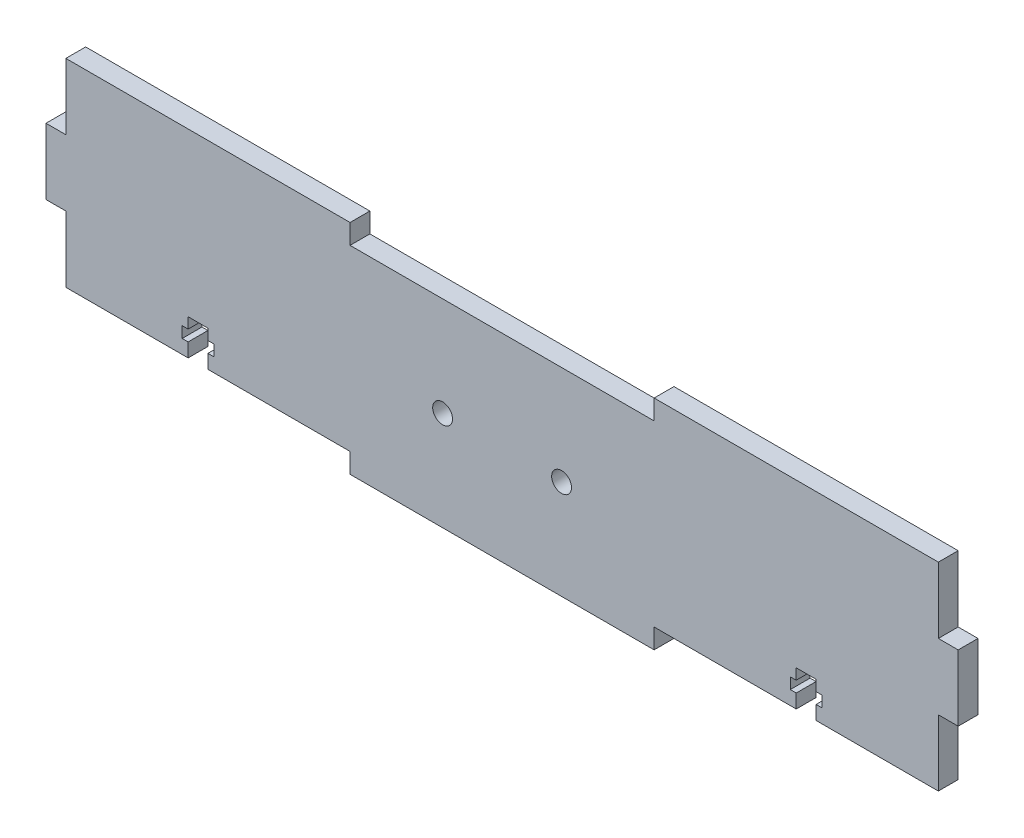
SolidWorks part; units mm, degrees
ref_plane "Alzado" through (0, 0, 0) normal (0, 0, 1) x (1, 0, 0)
ref_plane "Planta" through (0, 0, 0) normal (0, 1, 0) x (1, 0, 0)
ref_plane "Vista lateral" through (0, 0, 0) normal (1, 0, 0) x (0, 0, -1)
sketch "Croquis1" plane through (0, 0, 0) normal (0, 0, 1) x (1, 0, 0)
  line L0 (115, 0) -> (115, 23.3303) construction
  line L1 (0, 0) -> (230, 0)
  line L2 (0, 0) -> (0, 55)
  line L3 (0, 55) -> (230, 55)
  line L4 (230, 0) -> (230, 55)
  line L5 (0, 55) -> (5, 55)
  line L6 (0, 55) -> (0, 0)
  line L7 (0, 0) -> (5, 0)
  line L8 (5, 55) -> (5, 0)
  line L9 (225, 55) -> (225, 0)
  line L10 (76.6667, 5) -> (76.6667, 0)
  line L11 (0, 0) -> (230, 0)
  line L12 (0, 0) -> (0, 5)
  line L13 (0, 5) -> (230, 5)
  line L14 (230, 0) -> (230, 5)
  line L15 (153.3333, 0) -> (153.3333, 5)
  line L16 (0, 38.3333) -> (5, 38.3333)
  line L17 (5, 21.6667) -> (0, 21.6667)
  line L18 (225, 21.6667) -> (230, 21.6667)
  line L19 (230, 38.3333) -> (225, 38.3333)
  point P21 (2.5, 38.3333)
  dimension "D1" = 230
  dimension "D2" = 55
  dimension "D3" = 5
  dimension "D4" = 5
  dimension "D5" = 76.6667
  dimension "D6" = 76.6667
  dimension "D7" = 16.6667
  dimension "D8" = 16.6667
extrude "Saliente-Extruir1" add sketch "Croquis1" along normal blind 5
sketch "Croquis2" plane through (0, 0, 5) normal (0, 0, 1) x (1, 0, 0)
  line L0 (38.3333, 5) -> (38.3333, 14) construction
  line L1 (5, 5) -> (76.6667, 5) construction
  line L2 (115, 0) -> (115, 11.3726) construction
  line L3 (76.6667, 0) -> (153.3333, 0) construction
  line L4 (35.8333, 5) -> (35.8333, 8.5)
  line L5 (35.8333, 8.5) -> (34.3333, 8.5)
  line L6 (34.3333, 8.5) -> (34.3333, 11.3)
  line L7 (34.3333, 11.3) -> (35.8333, 11.3)
  line L8 (35.8333, 11.3) -> (35.8333, 14)
  line L9 (35.8333, 14) -> (40.8333, 14)
  line L10 (40.8333, 11.3) -> (40.8333, 14)
  line L11 (42.3333, 11.3) -> (40.8333, 11.3)
  line L12 (42.3333, 8.5) -> (42.3333, 11.3)
  line L13 (40.8333, 8.5) -> (42.3333, 8.5)
  line L14 (40.8333, 5) -> (40.8333, 8.5)
  line L15 (191.6667, 5) -> (191.6667, 14) construction
  line L16 (189.1667, 5) -> (189.1667, 8.5)
  line L17 (189.1667, 8.5) -> (187.6667, 8.5)
  line L18 (187.6667, 8.5) -> (187.6667, 11.3)
  line L19 (187.6667, 11.3) -> (189.1667, 11.3)
  line L20 (189.1667, 11.3) -> (189.1667, 14)
  line L21 (194.1667, 14) -> (189.1667, 14)
  line L22 (194.1667, 11.3) -> (194.1667, 14)
  line L23 (195.6667, 11.3) -> (194.1667, 11.3)
  line L24 (195.6667, 8.5) -> (195.6667, 11.3)
  line L25 (194.1667, 8.5) -> (195.6667, 8.5)
  line L26 (194.1667, 5) -> (194.1667, 8.5)
  line L27 (40.8333, 5) -> (35.8333, 5)
  line L28 (194.1667, 5) -> (189.1667, 5)
  line L29 (0, 21.6667) -> (0, 38.3333) construction
  point P10 (35.0833, 11.3)
  point P38 (38.3333, 9.5)
  dimension "D1" = 2.8
  dimension "D2" = 4
  dimension "D3" = 9
  dimension "D4" = 3.5
  dimension "D5" = 2.5
  dimension "D6" = 38.3333
extrude "Cortar-Extruir1" cut sketch "Croquis2" against normal blind 5
sketch "Croquis3" plane through (0, 0, 5) normal (0, 0, 1) x (1, 0, 0)
  line L0 (5, 55) -> (225, 55) construction
  line L1 (76.6667, 55) -> (153.3333, 55)
  line L2 (76.6667, 55) -> (76.6667, 50)
  line L3 (76.6667, 50) -> (153.3333, 50)
  line L4 (153.3333, 55) -> (153.3333, 50)
  line L5 (0, 21.6667) -> (0, 38.3333) construction
  line L6 (230, 21.6667) -> (230, 38.3333) construction
  dimension "D1" = 5
  dimension "D2" = 76.6667
  dimension "D3" = 76.6667
extrude "Cortar-Extruir2" cut sketch "Croquis3" against normal blind 10
sketch "Croquis4" plane through (0, 0, 5) normal (0, 0, 1) x (1, 0, 0)
  line L0 (115, 0) -> (115, 25) construction
  line L1 (76.6667, 0) -> (153.3333, 0) construction
  line L2 (100, 25) -> (115, 25) construction
  line L3 (40.8333, 5) -> (76.6667, 5) construction
  circle A0 centre (100, 25) radius 2.5
  circle A1 centre (130, 25) radius 2.5
  dimension "D1" = 5
  dimension "D2" = 15
  dimension "D3" = 20
extrude "Cortar-Extruir3" cut sketch "Croquis4" against normal blind 10
